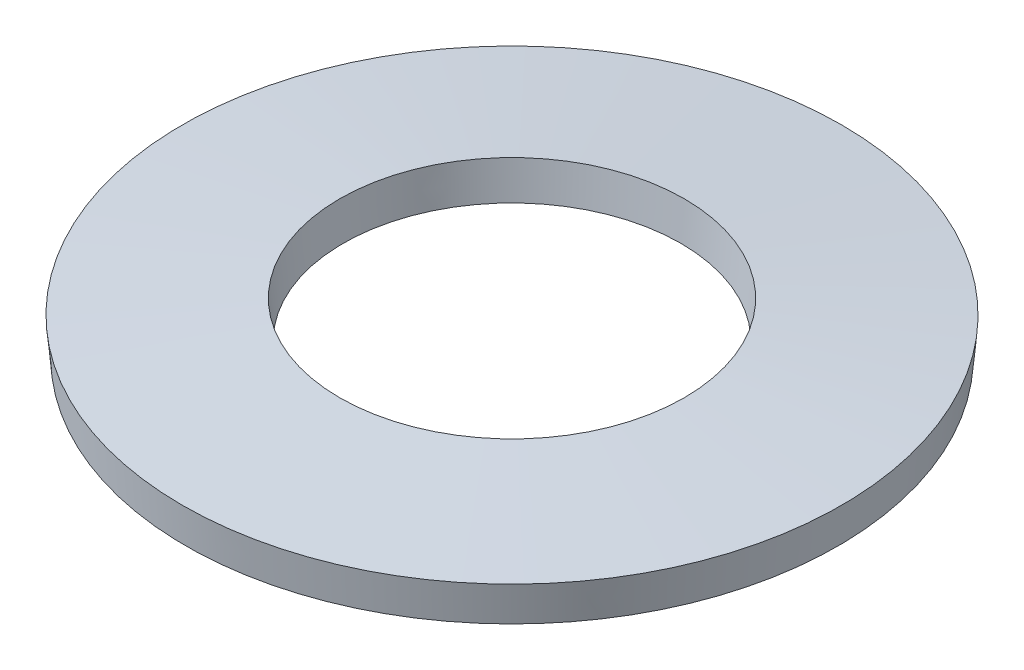
SolidWorks part; units mm, degrees
material "AISI 304"
ref_plane "Front Plane" through (0, 0, 0) normal (0, 0, 1) x (1, 0, 0)
ref_plane "Top Plane" through (0, 0, 0) normal (0, 1, 0) x (1, 0, 0)
ref_plane "Right Plane" through (0, 0, 0) normal (1, 0, 0) x (0, 0, -1)
sketch "Sketch1" plane through (0, 0, 0) normal (0, 0, 1) x (1, 0, 0)
  line L0 (7.9169, 0) -> (4.1, 0.3538)
  line L1 (4.1831, 1.25) -> (4.1, 0.3538)
  line L2 (4.1831, 1.25) -> (8, 0.8962)
  line L3 (7.9169, 0) -> (8, 0.8962)
  line L4 (0, 0) -> (0, 1.25) construction
  line L5 (0, 0) -> (7.9169, 0) construction
  line L6 (4.1, 0.3538) -> (0, 0.3538) construction
  line L7 (4.1, 0.3538) -> (4.1, 0) construction
  line L8 (4.1831, 1.25) -> (0, 1.25) construction
  line L9 (8, 0.8962) -> (8, 0) construction
  line L10 (8, 0) -> (7.9169, 0) construction
  dimension "D1" = 8.2
  dimension "D2" = 1.25
  dimension "D3" = 0.9
  dimension "D4" = 16
revolve "Revolve1" add sketch "Sketch1" angle 360 about L4
